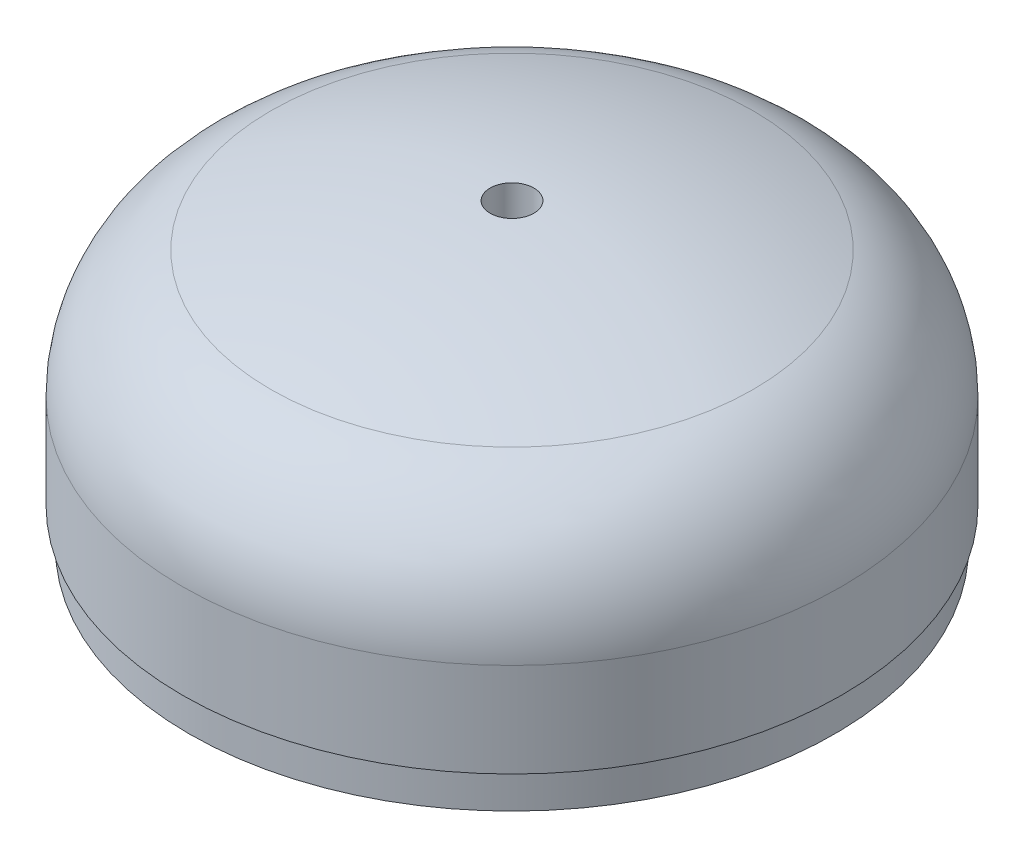
SolidWorks part; units mm, degrees
material "6061-T6 (SS)"
ref_plane "Front Plane" through (0, 0, 0) normal (0, 0, 1) x (1, 0, 0)
ref_plane "Top Plane" through (0, 0, 0) normal (0, 1, 0) x (1, 0, 0)
ref_plane "Right Plane" through (0, 0, 0) normal (1, 0, 0) x (0, 0, -1)
ref_axis "Axis1" through (0, 127.061, 0) along (0, -1, 0)
sketch "Sketch1" plane through (0, 0, 0) normal (0, 0, 1) x (1, 0, 0)
  line L0 (-63.5, 7.088) -> (-63.5, 25.2096)
  line L1 (-62.2217, 6.35) -> (-63.5, 7.088)
  line L2 (0, 127.061) -> (0, -81.9141) construction
  line L4 (-62.2217, 6.35) -> (-62.2217, 0)
  line L5 (-62.2217, 0) -> (-59.8405, 0)
  line L6 (55, 0) -> (-55, 0) construction
  line L8 (-63.5, 7.088) -> (-62.2217, 6.35)
  line L10 (-4.2164, 57.888) -> (-4.2164, 50.8994)
  line L15 (-59.8405, 0) -> (-59.8405, 6.35)
  line L16 (-59.8405, 6.35) -> (-56.515, 25.2096)
  arc A0 (-56.515, 25.2096) -> (-44.0765, 43.0755) centre (-37.465, 25.2096) cw
  arc A1 (-44.0765, 43.0755) -> (-4.2164, 50.8994) centre (0, -76.0306) cw
  arc A2 (-46.5007, 49.6263) -> (-63.5, 25.2096) centre (-37.465, 25.2096) ccw
  arc A3 (-46.5007, 49.6263) -> (-4.2164, 57.888) centre (0, -76.0306) cw
  point P14 (-61.0311, 0)
  dimension "D5" = 19.05
  dimension "D6" = 127
  dimension "D7" = 133.985
  dimension "D8" = 50.8
  dimension "D2" = 170
  dimension "D3" = 6.35
  dimension "D4" = 2.3813
  dimension "D9" = 63.5
  dimension "D13" = 4.2164
  dimension "D17" = 120
revolve "Revolve2" add sketch "Sketch1" angle 360 about axis through (0, 127.061, 0) along (0, -1, 0)
sketch "Sketch2" plane through (0, 0, 0) normal (0, 0, 1) x (1, 0, 0)
  line L0 (0, 127.061) -> (0, -81.9141) construction
  line L1 (0, 87.1374) -> (-97.8719, 87.1374)
  line L2 (0, 87.1374) -> (0, -26.2798)
  line L3 (0, -26.2798) -> (-97.8719, -26.2798)
  line L4 (-97.8719, 87.1374) -> (-97.8719, -26.2798)
revolve "Cut-Revolve1" [suppressed] cut sketch "Sketch2" angle 315 about axis through (0, 127.061, 0) along (0, -1, 0)
ref_plane "Plane2" through (0, 6.35, 0) normal (0, -1, 0) x (-1, 0, 0)
sketch "Sketch8" plane through (0, 0, 0) normal (0, 0, 1) x (1, 0, 0)
  line L0 (0, 127.061) -> (0, -81.9141) construction
  line L1 (0, 89.8009) -> (92.4947, 89.8009)
  line L2 (0, 89.8009) -> (0, -18.1338)
  line L3 (0, -18.1338) -> (92.4947, -18.1338)
  line L4 (92.4947, 89.8009) -> (92.4947, -18.1338)
revolve "Cut-Revolve2" [suppressed] cut sketch "Sketch8" angle 300 about axis through (0, 127.061, 0) along (0, -1, 0)
hole_wizard "1/4-20 Tapped Hole1" positions "Sketch9" profile "Sketch11" tap size "1/4-20" standard "ANSI Inch"
sketch "Sketch9" plane through (0, 58.9831, 0) normal (0, 1, 0) x (1, 0, 0)
  line L0 (-55, 0) -> (55, 0) construction
  circle A1 centre (0, 0) radius 63.5 construction
  point P0 (-58.7375, 0)
  dimension "D1" = 58.7375
sketch "Sketch11" plane through (-58.7375, 58.9831, 0) normal (1, 0, 0) x (0, 0, 1)
  line L0 (0, 0) -> (0, 14.2338)
  line L1 (0, 14.2338) -> (2.5527, 12.7)
  line L2 (2.5527, 12.7) -> (2.5527, 0)
  line L5 (2.5527, 0) -> (0, 0)
  line L10 (0, 14.2338) -> (-2.5527, 12.7) construction
  line L11 (0, -6.35) -> (0, 107.95) construction
  dimension "Tap Drill Dia." = 5.1054
  dimension "Tap Drill Depth" = 12.7
  dimension "Drill Angle" = 118
pattern_circular "CirPattern1" [suppressed] count 6 over 360 about axis through (0, 127.061, 0) along (0, -1, 0)
